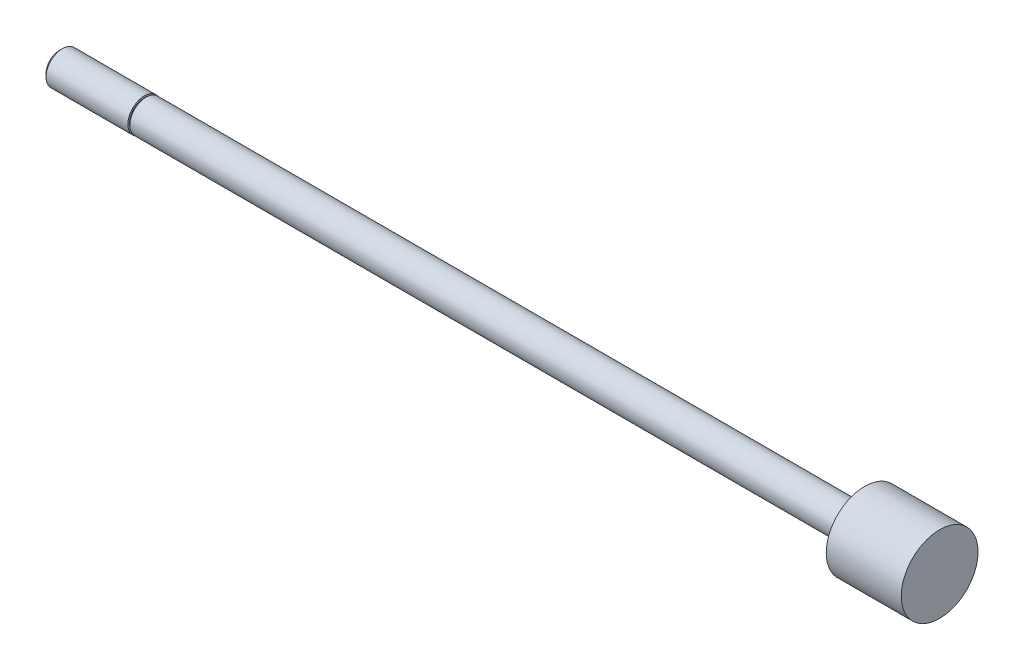
SolidWorks part; units mm, degrees
ref_plane "Front Plane" through (0, 0, 0) normal (0, 0, 1) x (1, 0, 0)
ref_plane "Top Plane" through (0, 0, 0) normal (0, 1, 0) x (1, 0, 0)
ref_plane "Right Plane" through (0, 0, 0) normal (1, 0, 0) x (0, 0, -1)
ref_plane "Plane1" through (0, 0, 0) normal (0, 0, 1) x (1, 0, 0)
sketch "Sketch1" plane through (0, 0, 0) normal (0, 0, 1) x (1, 0, 0)
  line L0 (0, 0) -> (0, 2.3749)
  line L1 (0, 2.3749) -> (105.1052, 2.3749)
  line L2 (105.1052, 2.3749) -> (105.1052, 5.6197)
  line L3 (105.1052, 5.6197) -> (116.078, 5.6197)
  line L4 (116.078, 5.6197) -> (116.078, 0)
  line L5 (116.078, 0) -> (0, 0)
  line L6 (116.078, 0) -> (0, 0) construction
revolve "Revolve1" add sketch "Sketch1" angle 360 about L6
ref_plane "Plane2" through (0, 0, 0) normal (0, 0, 1) x (1, 0, 0)
sketch "Sketch2" plane through (0, 0, 0) normal (0, 0, 1) x (1, 0, 0)
  line L0 (-12.7, 0) -> (-12.7, 1.9406)
  line L1 (-12.7, 1.9406) -> (-12.2276, 2.413)
  line L2 (-12.2276, 2.413) -> (0, 2.413)
  line L3 (0, 2.413) -> (0, 0)
  line L4 (0, 0) -> (-12.7, 0)
  line L5 (0, 0) -> (-12.7, 0) construction
revolve "Revolve2" add sketch "Sketch2" angle 360 about L5
cosmetic thread "Cosmetic Thread1" parameters "D1"=12.7, "D2"=3.8811
ref_plane "Plane3" through (0, 0, 0) normal (0, 0, 1) x (1, 0, 0)
sketch "Sketch3" plane through (0, 0, 0) normal (0, 0, 1) x (1, 0, 0)
  line L0 (-0.254, 2.159) -> (0, 2.159)
  line L1 (0, 2.159) -> (0, 2.667)
  line L2 (0, 2.667) -> (-0.254, 2.667)
  line L3 (-0.254, 2.667) -> (-0.254, 2.159)
  line L4 (0, 0) -> (-0.254, 0) construction
revolve "Cut-Revolve1" cut sketch "Sketch3" angle 360 about L4
